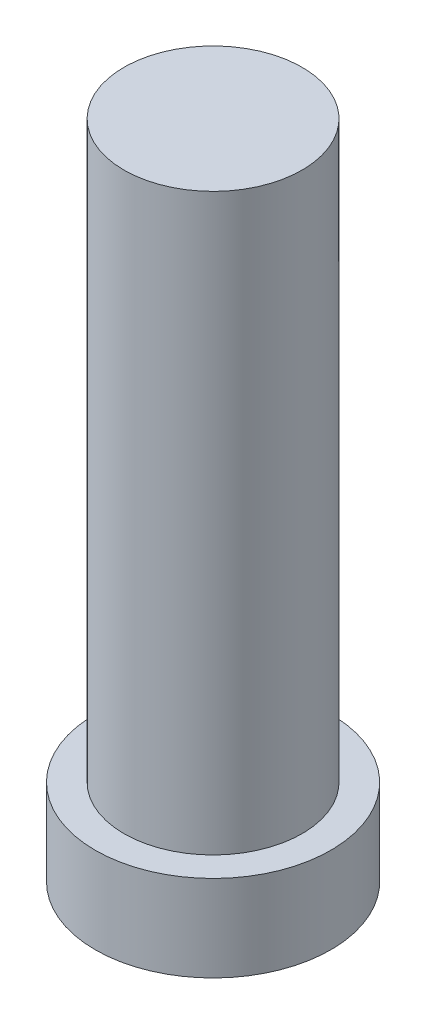
SolidWorks part; units mm, degrees
ref_plane "Front Plane" through (0, 0, 0) normal (0, 0, 1) x (1, 0, 0)
ref_plane "Top Plane" through (0, 0, 0) normal (0, 1, 0) x (1, 0, 0)
ref_plane "Right Plane" through (0, 0, 0) normal (1, 0, 0) x (0, 0, -1)
sketch "Sketch1" plane through (0, 0, 0) normal (0, 1, 0) x (1, 0, 0)
  circle A0 centre (0, 0) radius 5.207
  dimension "D1" = 10.414
extrude "Boss-Extrude1" add sketch "Sketch1" along normal blind 3.81
sketch "Sketch2" plane through (0, 3.81, 0) normal (0, 1, 0) x (1, 0, 0)
  circle A0 centre (0, 0) radius 3.937
  dimension "D1" = 7.874
extrude "Boss-Extrude2" add sketch "Sketch2" along normal blind 25.4
